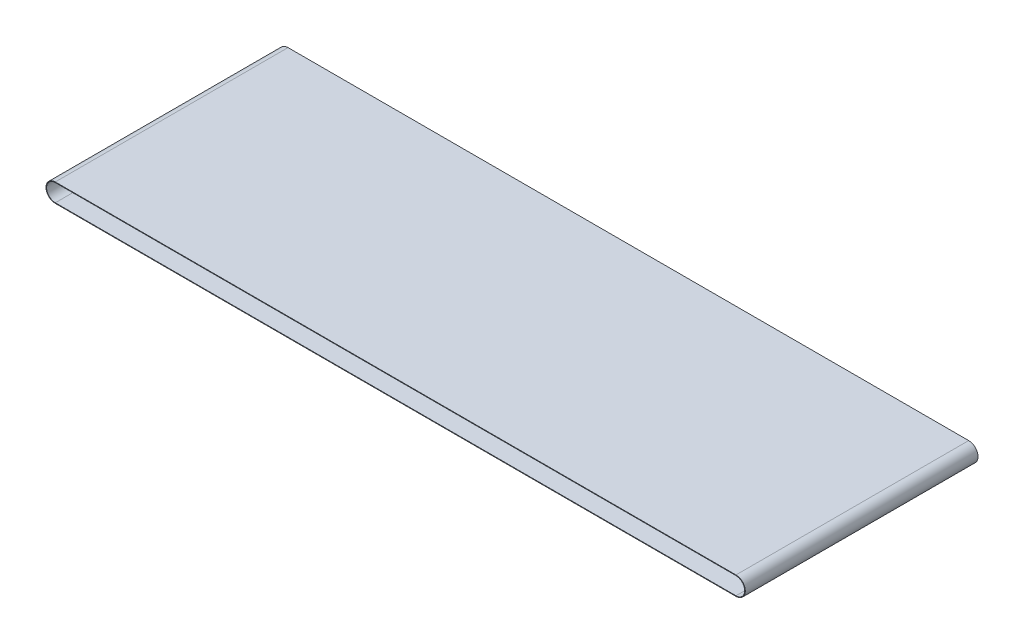
SolidWorks part; units mm, degrees
ref_plane "Front" through (0, 0, 0) normal (0, 0, 1) x (1, 0, 0)
ref_plane "Top" through (0, 0, 0) normal (0, 1, 0) x (1, 0, 0)
ref_plane "Right" through (0, 0, 0) normal (1, 0, 0) x (0, 0, -1)
sketch "Sketch1" plane through (0, 0, 0) normal (0, 0, 1) x (1, 0, 0)
  line L0 (-585, 0) -> (585, 0)
  line L1 (0, 72.5805) -> (0, -67.8405) construction
  line L2 (-585, -30) -> (585, -30)
  arc A0 (-585, 0) -> (-585, -30) centre (-585, -15) ccw
  arc A1 (585, 0) -> (585, -30) centre (585, -15) cw
  dimension "D1" = 15
  dimension "D2" = 1200
extrude "Extrude-Thin1" add sketch "Sketch1" along normal mid plane 400 thin thin type one direction wall 1
